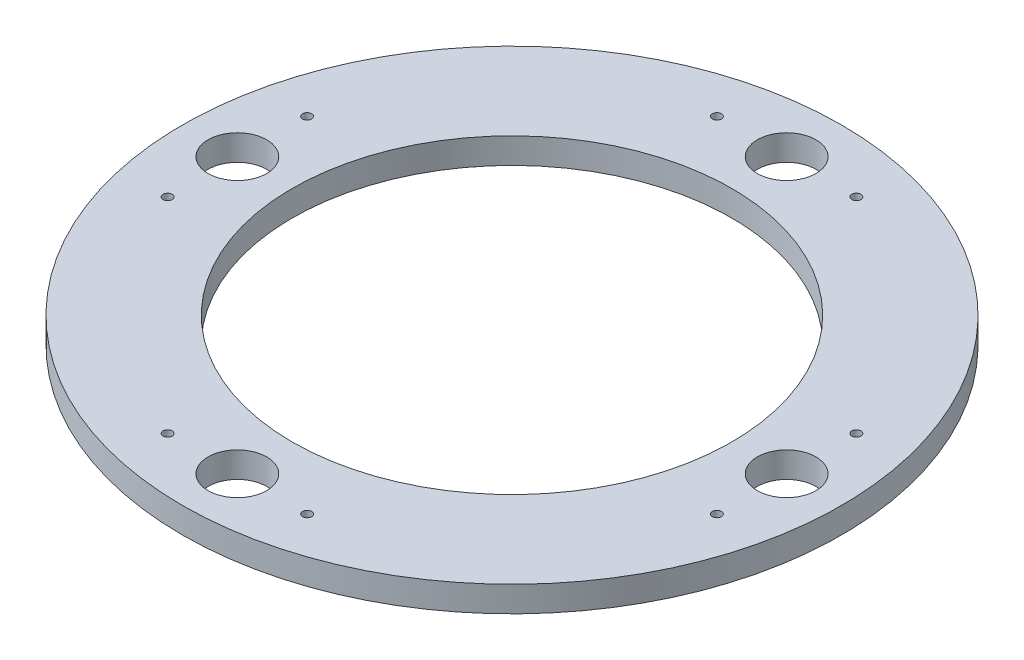
SolidWorks part; units mm, degrees
material "AISI 304"
ref_plane "前视基准面" through (0, 0, 0) normal (0, 0, 1) x (1, 0, 0)
ref_plane "上视基准面" through (0, 0, 0) normal (0, 1, 0) x (1, 0, 0)
ref_plane "右视基准面" through (0, 0, 0) normal (1, 0, 0) x (0, 0, -1)
sketch "Sketch2" plane through (0, 0, 0) normal (0, 1, 0) x (1, 0, 0)
  circle A0 centre (0, 0) radius 90
extrude "Extrude1" add sketch "Sketch2" along normal blind 7
sketch "Sketch3" plane through (0, 7, 0) normal (0, 1, 0) x (1, 0, 0)
  circle A0 centre (0, 75) radius 8
  dimension "D1" = 75
extrude "Cut-Extrude1" cut sketch "Sketch3" against normal through all
sketch "Sketch6" plane through (0, 7, 0) normal (0, 1, 0) x (1, 0, 0)
  circle A0 centre (0, 75) radius 8 construction
  point P0 (0, 75)
hole_wizard "M3x0.5 Tapped Hole1" positions "Sketch4" profile "Sketch5" tap size "M3x0.5" standard "ANSI Metric" end condition through all
sketch "Sketch4" plane through (0, 7, 0) normal (0, 1, 0) x (1, 0, 0)
  circle A0 centre (0, 75) radius 8 construction
  point P0 (-19.05, 75)
  point P2 (19.05, 75)
  dimension "D1" = 38.1
  dimension "D2" = 19.05
sketch "Sketch5" plane through (-19.05, 7, -75) normal (1, 0, 0) x (0, 0, 1)
  line L0 (0, 0) -> (0, 7)
  line L1 (0, 7) -> (1.25, 7)
  line L2 (1.25, 7) -> (1.25, 0)
  line L5 (1.25, 0) -> (0, 0)
  line L11 (0, -6.35) -> (0, 107.95) construction
  dimension "Thru Tap Drill Dia." = 2.5
  dimension "Thru Tap Drill Depth" = 7
cosmetic thread "Hole Thread1" parameters "D2"=3
cosmetic thread "Hole Thread2" parameters "D2"=3
pattern_circular "CirPattern1" count 4 every 90 about axis through (0, 0, 0) along (0, 1, 0) of "M3x0.5 Tapped Hole1", "Cut-Extrude1"
sketch "Sketch7" plane through (0, 7, 0) normal (0, 1, 0) x (1, 0, 0)
  line L0 (0, 75) -> (75, 0) construction
sketch "Sketch8" plane through (0, 7, 0) normal (0, 1, 0) x (1, 0, 0)
  circle A0 centre (0, 0) radius 60
extrude "Cut-Extrude2" cut sketch "Sketch8" against normal through all
